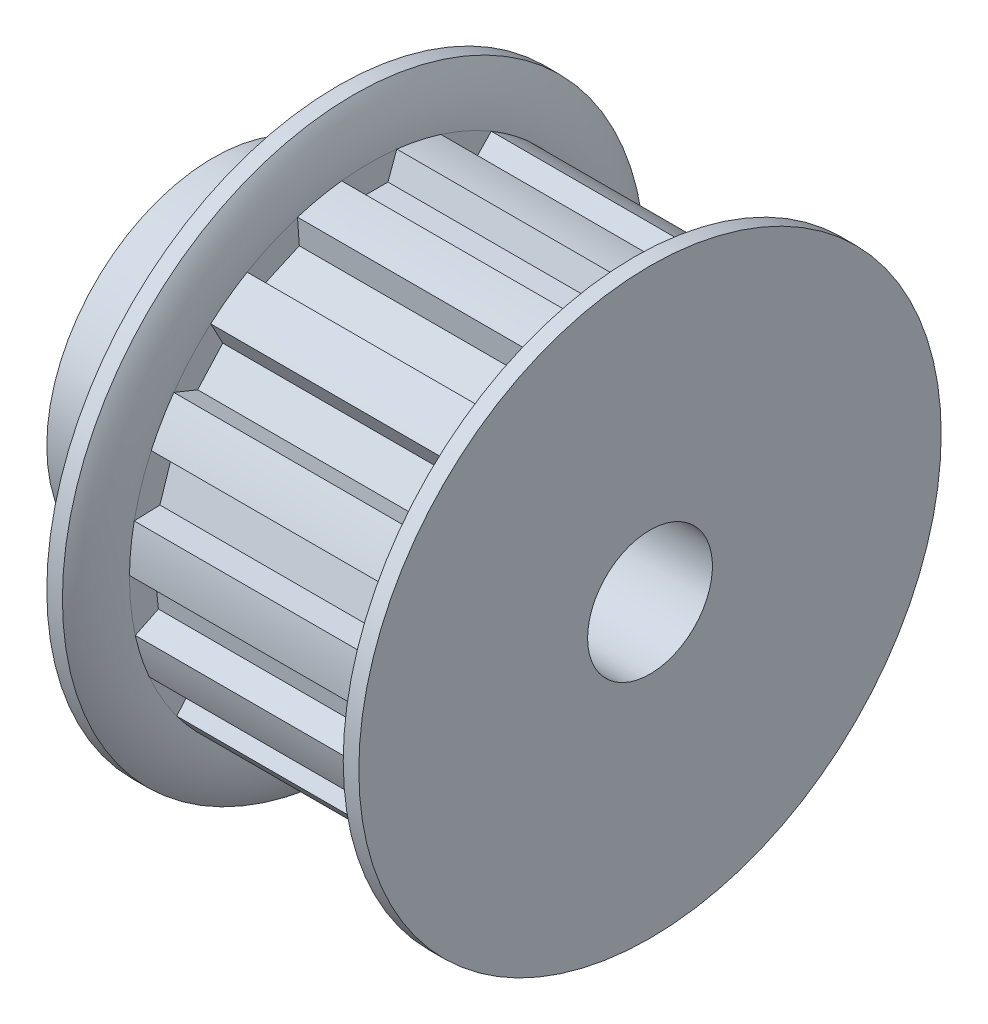
SolidWorks part; units mm, degrees
ref_plane "Front Plane" through (0, 0, 0) normal (0, 0, 1) x (1, 0, 0)
ref_plane "Top Plane" through (0, 0, 0) normal (0, 1, 0) x (1, 0, 0)
ref_plane "Right Plane" through (0, 0, 0) normal (1, 0, 0) x (0, 0, -1)
sketch "Sketch2" plane through (0, 0, 0) normal (1, 0, 0) x (0, 0, -1)
  line L3 (0, 0) -> (0, 10.325) construction
  line L6 (0, 10.325) -> (0, 11.525) construction
  line L7 (-1.325, 11.4486) -> (-0.9017, 10.2856)
  line L8 (1.325, 11.4486) -> (0.9017, 10.2856)
  line L9 (0, -2.2) -> (0, -3.2) construction
  line L10 (0, 12.025) -> (0, 11.525) construction
  line L12 (-0.9017, 10.2856) -> (0.9017, 10.2856)
  line L15 (0, 0) -> (0, -2.2) construction
  circle A0 centre (0, 0) radius 12.025 construction
  circle A1 centre (0, 0) radius 10.325 construction
  arc A7 (1.325, 11.4486) -> (-1.325, 11.4486) centre (0, 0) ccw
  dimension "D1" = 40
  dimension "D3" = 0.5
  dimension "D2" = 1.2
  dimension "D4" = 2.65
sketch "Sketch1" plane through (0, 0, 0) normal (0, 0, 1) x (1, 0, 0)
  line L0 (-10.5, 0) -> (10.5, 0) construction
  line L1 (-10.5, 3) -> (10.5, 3)
  line L2 (-10.5, 3) -> (-10.5, 8)
  line L3 (-4.5, 14) -> (-3.75, 14)
  line L4 (-3, 11.525) -> (-4.5, 11.525) construction
  line L5 (9.75, 11.525) -> (9.75, 14) construction
  line L6 (-3, 11.525) -> (9, 11.525)
  line L8 (9, 11.525) -> (10.5, 11.525) construction
  line L9 (9.75, 14) -> (10.5, 14)
  line L10 (10.5, 14) -> (10.5, 3)
  line L12 (-7.5, 8) -> (-7.5, 3) construction
  line L13 (-4.5, 14) -> (-4.5, 8)
  line L14 (-4.5, 8) -> (-10.5, 8)
  arc A0 (9, 11.525) -> (9.75, 14) centre (13.4588, 11.525) cw
  arc A1 (-3, 11.525) -> (-3.75, 14) centre (-7.4588, 11.525) ccw
  dimension "Bore Size" = 6
  dimension "Overall Width" = 21
  dimension "Inside Width" = 12
  dimension "Outside Width" = 15
  dimension "Hub Dia" = 16
  dimension "OD" = 28
revolve "Revolve1" add sketch "Sketch1" angle 360 mid plane about L0
sketch "Sketch3" plane through (0, 0, 0) normal (1, 0, 0) x (0, 0, -1)
  line L2 (-1.325, 11.4486) -> (-0.9017, 10.2856) construction
  line L3 (-0.9017, 10.2856) -> (0.9017, 10.2856) construction
  line L4 (1.325, 11.4486) -> (0.9017, 10.2856) construction
  line L5 (-1.325, 11.4486) -> (-0.9017, 10.2856)
  line L6 (-0.9017, 10.2856) -> (0.9017, 10.2856)
  line L7 (1.325, 11.4486) -> (0.9017, 10.2856)
  arc A1 (1.325, 11.4486) -> (-1.325, 11.4486) centre (0, 0) ccw construction
  arc A2 (1.325, 11.4486) -> (-1.325, 11.4486) centre (0, 0) ccw
extrude "Cut-Extrude1" cut sketch "Sketch3" along normal up to vertex (12 mm away) from vertex at -3 up to point (9, 11.525, 0) starting at point (-3, 11.525, 0)
pattern_circular "CirPattern1" count 15 over 360 about axis through (0, 0, 0) along (1, 0, 0) of "Cut-Extrude1"
sketch "Sketch5" plane through (0, 0, 0) normal (0, 0, 1) x (1, 0, 0)
  line L0 (9, -8.4833) -> (9, -10.0409) construction
  point P0 (9, 0)
equation "\"D3@Sketch2\" = \"ht@Sketch2\"/2"
equation "\"D2@Sketch2\" = \"hs@Sketch2\"-\"ht@Sketch2\""
